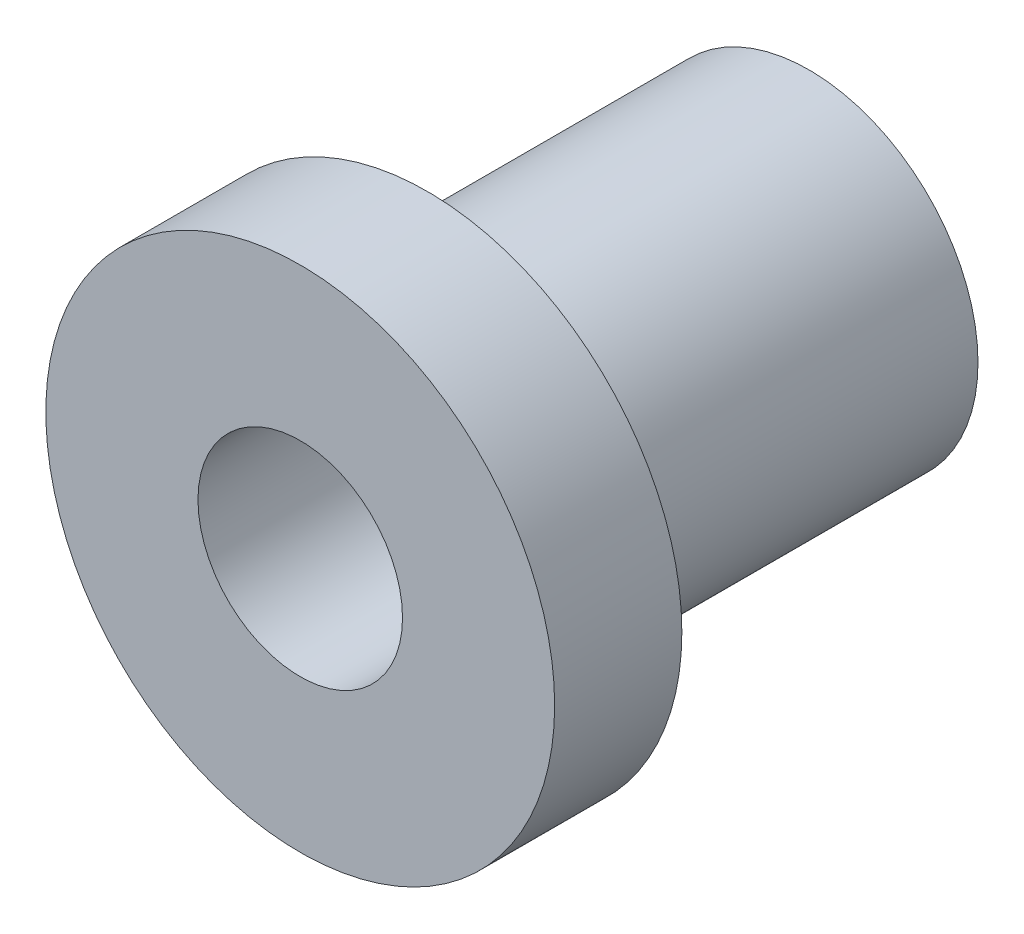
SolidWorks part; units mm, degrees
material "Brass"
ref_plane "Front Plane" through (0, 0, 0) normal (0, 0, 1) x (1, 0, 0)
ref_plane "Top Plane" through (0, 0, 0) normal (0, 1, 0) x (1, 0, 0)
ref_plane "Right Plane" through (0, 0, 0) normal (1, 0, 0) x (0, 0, -1)
sketch "Sketch1" plane through (0, 0, 0) normal (0, 0, 1) x (1, 0, 0)
  circle A0 centre (0, 0) radius 4.2164
  dimension "D1" = 8.4328
extrude "Boss-Extrude1" add sketch "Sketch1" along normal blind 9.525
sketch "Sketch2" plane through (0, 0, 9.525) normal (0, 0, 1) x (1, 0, 0)
  circle A0 centre (0, 0) radius 6.35
  dimension "D1" = 12.7
extrude "Boss-Extrude2" add sketch "Sketch2" along normal blind 3.175
sketch "Sketch3" plane through (0, 0, 12.7) normal (0, 0, 1) x (1, 0, 0)
  circle A0 centre (0, 0) radius 2.5527
  dimension "D1" = 5.1054
extrude "Cut-Extrude1" cut sketch "Sketch3" against normal through all
